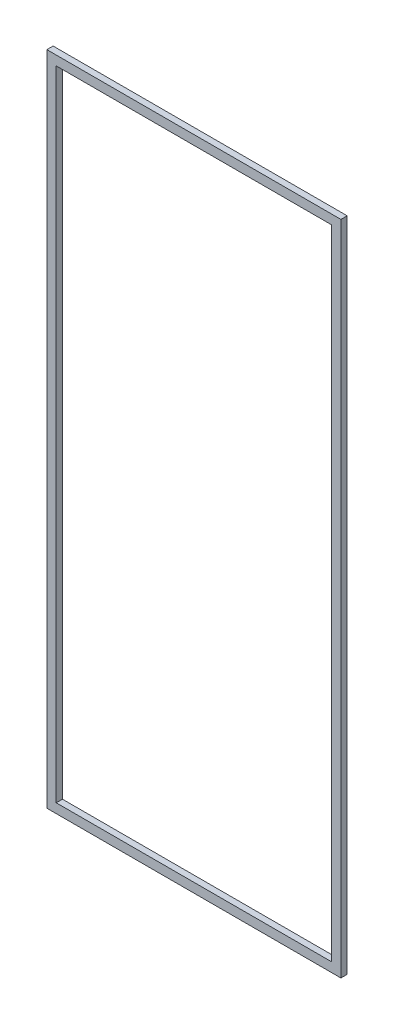
SolidWorks part; units mm, degrees
ref_plane "Спереди" through (0, 0, 0) normal (0, 0, 1) x (1, 0, 0)
ref_plane "Сверху" through (0, 0, 0) normal (0, 1, 0) x (1, 0, 0)
ref_plane "Справа" through (0, 0, 0) normal (1, 0, 0) x (0, 0, -1)
sketch "Эскиз1" plane through (0, 0, 0) normal (0, 0, 1) x (1, 0, 0)
  line L1 (-235, 525) -> (235, 525)
  line L2 (-235, 525) -> (-235, -525)
  line L3 (-235, -525) -> (235, -525)
  line L4 (235, 525) -> (235, -525)
  line L5 (-235, 525) -> (235, -525) construction
  line L6 (-235, -525) -> (235, 525) construction
  point P0 (0, 0)
extrude "Вытянуть-Тонкостенный1" add sketch "Эскиз1" along normal blind 10 thin
